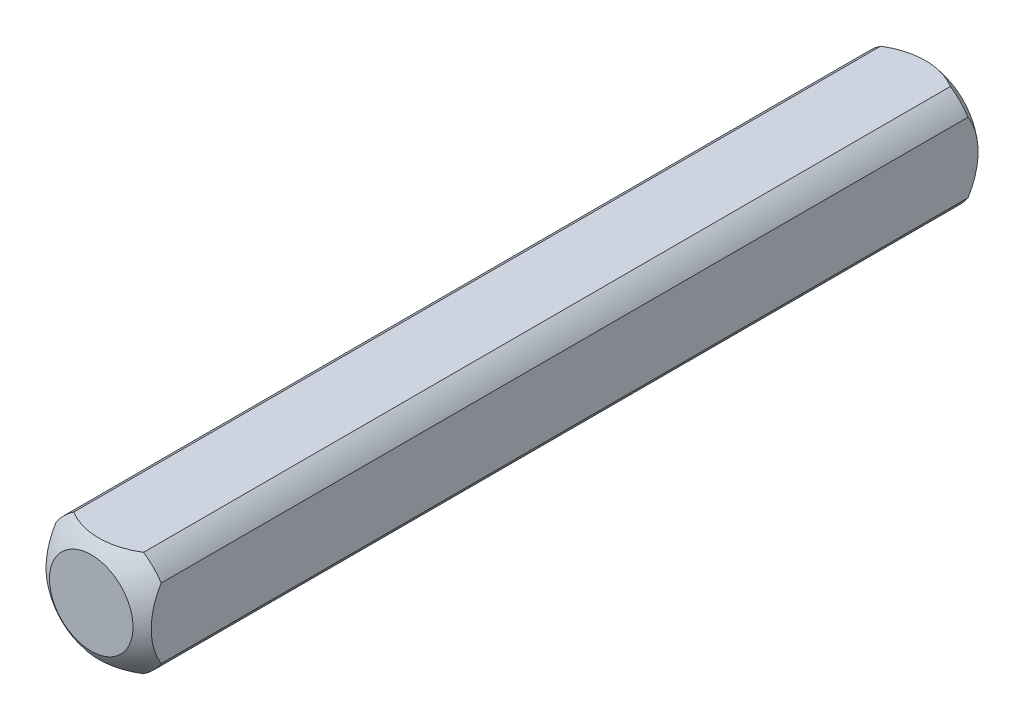
SolidWorks part; units mm, degrees
material "Custom Plastic"
ref_plane "Front Plane" through (0, 0, 0) normal (0, 0, 1) x (1, 0, 0)
ref_plane "Top Plane" through (0, 0, 0) normal (0, 1, 0) x (1, 0, 0)
ref_plane "Right Plane" through (0, 0, 0) normal (1, 0, 0) x (0, 0, -1)
sketch "Sketch1" plane through (0, 0, 0) normal (0, 0, 1) x (1, 0, 0)
  line L0 (-3.175, -3.175) -> (3.175, 3.175) construction
  line L1 (-3.175, -3.175) -> (3.175, -3.175)
  line L2 (-3.175, -3.175) -> (-3.175, 3.175)
  line L3 (-3.175, 3.175) -> (3.175, 3.175)
  line L4 (3.175, -3.175) -> (3.175, 3.175)
  dimension "D1" = 6.35
extrude "Boss-Extrude1" add sketch "Sketch1" along normal blind 25.4
sketch "Sketch2" plane through (0, 0, 0) normal (0, 0, -1) x (-1, 0, 0)
  circle A0 centre (0, 0) radius 3.81
  dimension "D1" = 7.62
extrude "Cut-Extrude1" cut sketch "Sketch2" against normal through all flip side to cut
ref_axis "Axis1" through (0, 0, 25.4) along (0, 0, -1)
sketch "Sketch3" plane through (0, 0, 0) normal (0, 1, 0) x (1, 0, 0)
  line L1 (-5.0537, -3.8933) -> (-5.0537, 5.7405)
  line L2 (-5.0537, 5.7405) -> (0, 5.7405)
  line L5 (0, -25.4) -> (0, 0) construction
  line L8 (0, 0.6703) -> (0, 5.7405)
  arc A0 (-5.0537, -3.8933) -> (0, 0.6703) centre (0, -4.4097) cw
  dimension "D1" = 5.08
revolve "Cut-Revolve1" cut sketch "Sketch3" angle 360 about axis through (0, 0, 25.4) along (0, 0, -1)
mirror "Mirror1" about plane through (0, 0, 25.4) normal (0, 0, -1) of bodies 103
